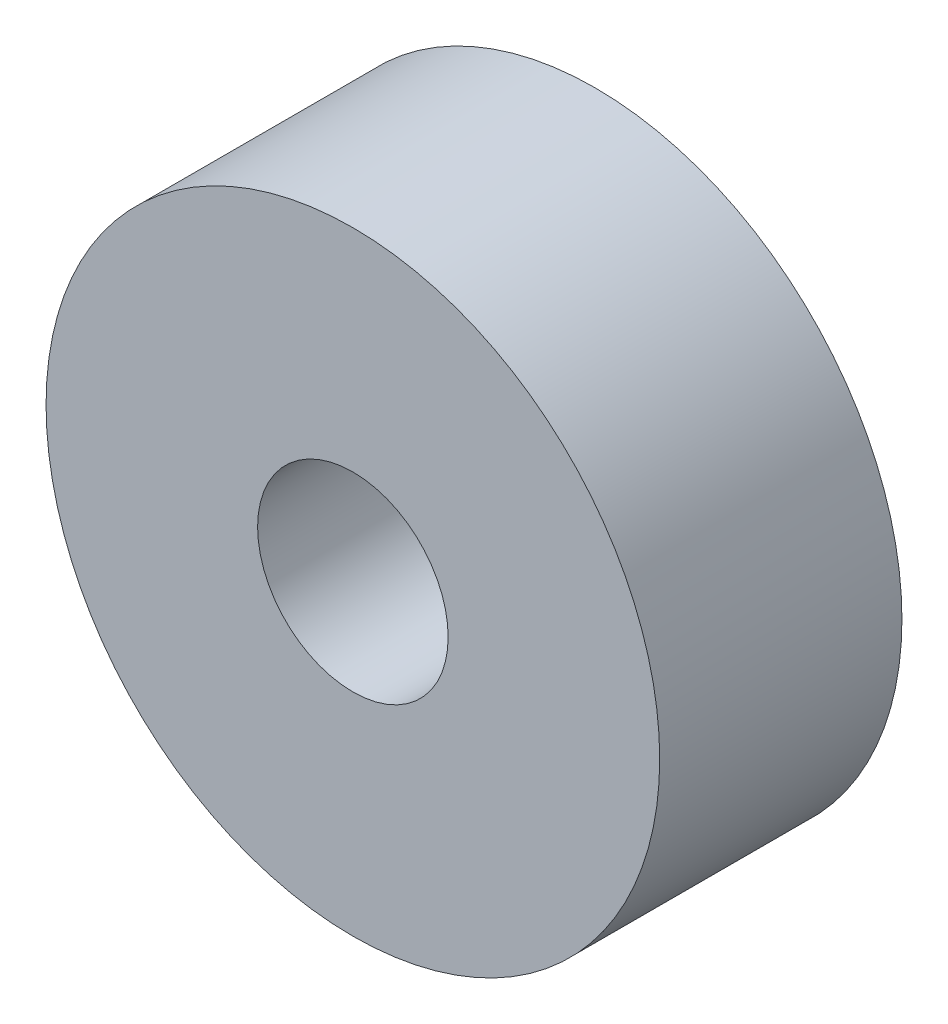
SolidWorks part; units mm, degrees
ref_plane "Front Plane" through (0, 0, 0) normal (0, 0, 1) x (1, 0, 0)
ref_plane "Top Plane" through (0, 0, 0) normal (0, 1, 0) x (1, 0, 0)
ref_plane "Right Plane" through (0, 0, 0) normal (1, 0, 0) x (0, 0, -1)
sketch "Sketch1" plane through (0, 0, 0) normal (0, 0, 1) x (1, 0, 0)
  circle A0 centre (0, 0) radius 9.5
  dimension "D1" = 19
extrude "Main Extrude" add sketch "Sketch1" along normal blind 7.5
sketch "Sketch2" plane through (0, 0, 7.5) normal (0, 0, 1) x (1, 0, 0)
  circle A0 centre (0, 0) radius 2.95
  dimension "D1" = 5.9
ref_plane "Halfway front plane" through (0, 0, 3) normal (0, 0, 1) x (1, 0, 0)
extrude "Cut-Extrude1" cut sketch "Sketch2" against normal blind 10
